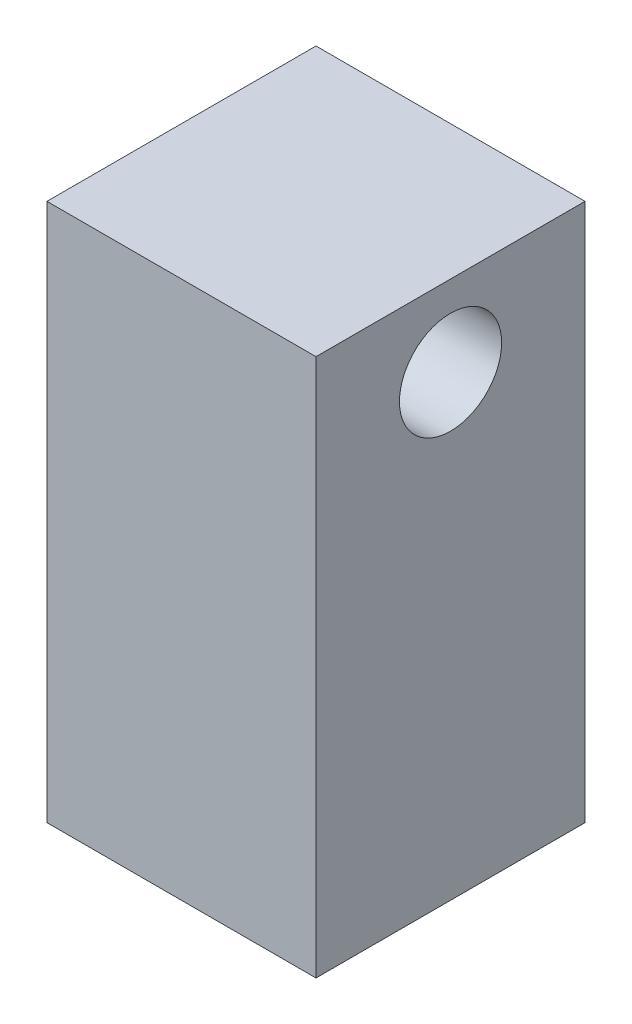
SolidWorks part; units mm, degrees
ref_plane "Front Plane" through (0, 0, 0) normal (0, 0, 1) x (1, 0, 0)
ref_plane "Top Plane" through (0, 0, 0) normal (0, 1, 0) x (1, 0, 0)
ref_plane "Right Plane" through (0, 0, 0) normal (1, 0, 0) x (0, 0, -1)
sketch "Sketch1" plane through (0, 0, 0) normal (0, 1, 0) x (1, 0, 0)
  line L1 (14.8268, -51.1747) -> (4.8268, -51.1747)
  line L2 (14.8268, -51.1747) -> (14.8268, -41.1747)
  line L3 (14.8268, -41.1747) -> (4.8268, -41.1747)
  line L4 (4.8268, -51.1747) -> (4.8268, -41.1747)
  dimension "D1" = 10
  dimension "D2" = 10
extrude "Boss-Extrude1" add sketch "Sketch1" against normal blind 20
sketch "Sketch2" plane through (4.8268, 0, 0) normal (-1, 0, 0) x (0, 0, 1)
  line L0 (41.1747, -20) -> (51.1747, -20) construction
  line L1 (42.6747, -11) -> (49.6747, -11)
  line L2 (42.6747, -11) -> (42.6747, -18)
  line L3 (42.6747, -18) -> (49.6747, -18)
  line L4 (49.6747, -11) -> (49.6747, -18)
  line L5 (41.1747, -20) -> (41.1747, 0) construction
  line L6 (51.1747, -20) -> (51.1747, 0) construction
  dimension "D1" = 2
  dimension "D2" = 1.5
  dimension "D3" = 1.5
  dimension "D4" = 7
hole_wizard "#6 Clearance Hole1" positions "3DSketch1" profile "Sketch3" hole size "#6" standard "ANSI Inch"
sketch3d "3DSketch1"
  line L0 (4.8268, -20, 41.1747) -> (4.8268, 0, 41.1747) construction
  line L1 (4.8268, 0, 41.1747) -> (4.8268, 0, 51.1747) construction
  point P0 (4.8268, -3, 46.1747)
  dimension "D1" = 5
  dimension "D2" = 3
sketch "Sketch3" plane through (4.8268, -3, 46.1747) normal (0, 1, 0) x (0, 0, 1)
  line L0 (0, 0) -> (0, 18.1408)
  line L1 (0, 18.1408) -> (1.8986, 17)
  line L2 (1.8986, 17) -> (1.8986, 0)
  line L5 (1.8986, 0) -> (0, 0)
  line L10 (0, 18.1408) -> (-1.8987, 17) construction
  line L11 (0, -6.35) -> (0, 107.95) construction
  dimension "Hole Dia." = 3.7973
  dimension "Hole Depth" = 17
  dimension "Drill Angle" = 118
extrude "Cut-Extrude1" cut sketch "Sketch2" against normal blind 7
